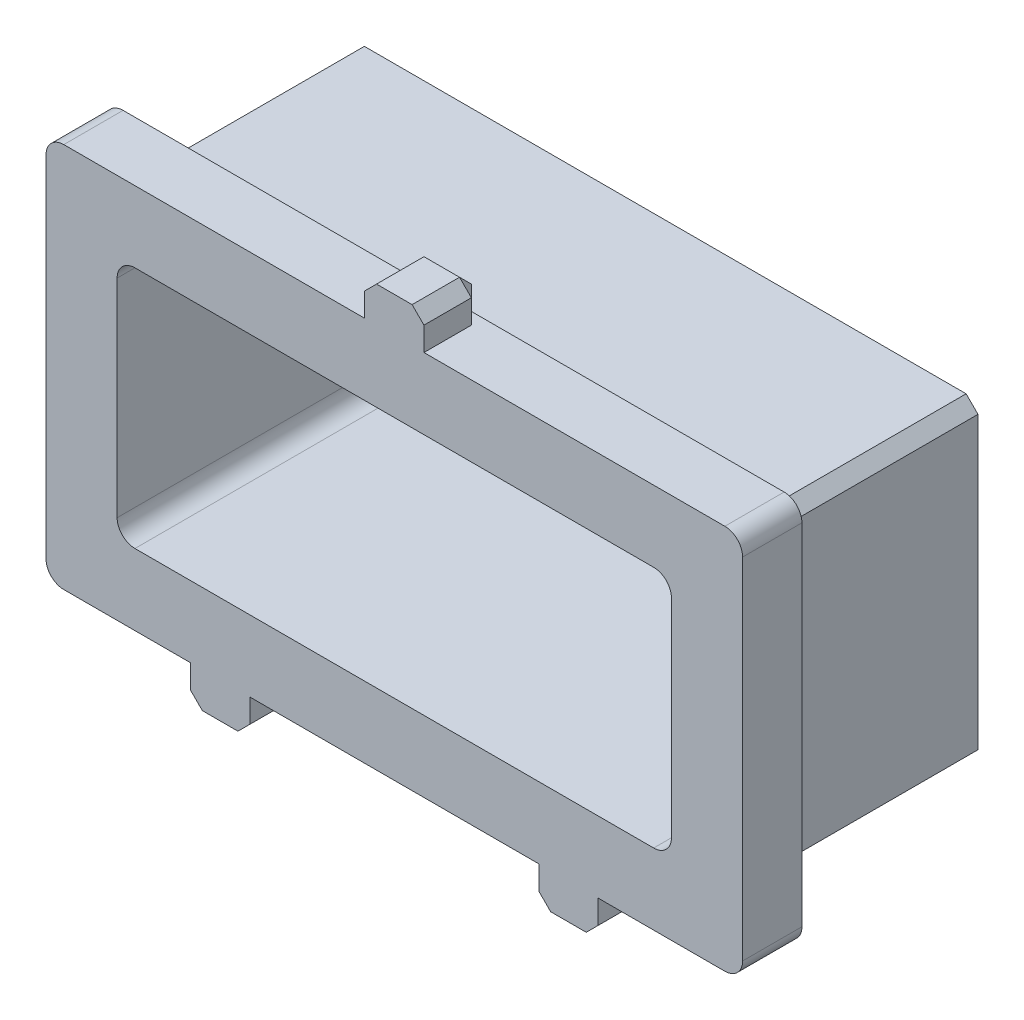
SolidWorks part; units mm, degrees
ref_plane "Front Plane" through (0, 0, 0) normal (0, 0, 1) x (1, 0, 0)
ref_plane "Top Plane" through (0, 0, 0) normal (0, 1, 0) x (1, 0, 0)
ref_plane "Right Plane" through (0, 0, 0) normal (1, 0, 0) x (0, 0, -1)
sketch "Sketch1" plane through (0, 0, 0) normal (0, 0, 1) x (1, 0, 0)
  line L4 (29.8204, 195.8186) -> (29.8204, 202.5496)
  line L5 (29.8204, 202.5496) -> (16.4219, 202.5496)
  line L6 (16.4219, 202.5496) -> (16.4219, 195.8186)
  line L7 (16.4219, 195.8186) -> (29.8204, 195.8186)
  line L8 (29.8204, 195.8186) -> (29.8204, 202.5496)
  line L9 (29.8204, 202.5496) -> (16.4219, 202.5496)
  line L10 (16.4219, 202.5496) -> (16.4219, 195.8186)
  line L11 (16.4219, 195.8186) -> (29.8204, 195.8186)
  dimension "D1" = 0
extrude "Extrude-Thin1" add sketch "Sketch1" along normal blind 5.8039 thin thin type one direction reverse wall 0.762
sketch "Sketch2" plane through (0, 0, 5.8039) normal (0, 0, 1) x (1, 0, 0)
  line L4 (16.4219, 195.8186) -> (29.8204, 195.8186)
  line L5 (29.8204, 195.8186) -> (29.8204, 202.5496)
  line L6 (29.8204, 202.5496) -> (16.4219, 202.5496)
  line L7 (16.4219, 202.5496) -> (16.4219, 195.8186)
  line L8 (16.4219, 195.8186) -> (29.8204, 195.8186)
  line L9 (29.8204, 195.8186) -> (29.8204, 202.5496)
  line L10 (29.8204, 202.5496) -> (16.4219, 202.5496)
  line L11 (16.4219, 202.5496) -> (16.4219, 195.8186)
  dimension "D1" = 0
extrude "Extrude-Thin2" add sketch "Sketch2" against normal blind 1.27 thin
sketch "Sketch4" plane through (0, 0, 5.8039) normal (0, 0, 1) x (1, 0, 0)
  line L0 (15.6599, 203.3116) -> (23.1211, 203.3116) construction
  line L1 (30.5824, 203.3116) -> (15.6599, 203.3116) construction
  line L2 (23.1211, 203.3116) -> (30.5824, 203.3116) construction
  line L3 (23.1211, 203.3116) -> (23.1211, 204.0736) construction
  line L4 (23.1211, 203.3116) -> (23.1211, 204.0736) construction
  line L5 (15.6599, 195.0566) -> (30.5824, 195.0566) construction
  line L6 (23.7561, 203.3116) -> (23.7561, 204.0736)
  line L7 (15.6599, 195.0566) -> (19.3905, 195.0566) construction
  line L8 (22.4861, 203.3116) -> (22.4861, 204.0736)
  line L9 (19.3905, 195.0566) -> (23.1211, 195.0566) construction
  line L10 (23.1211, 195.0566) -> (26.8517, 195.0566) construction
  line L11 (23.7561, 203.3116) -> (22.4861, 203.3116)
  line L12 (23.7561, 204.0736) -> (22.4861, 204.0736)
  line L13 (26.8517, 195.0566) -> (30.5824, 195.0566) construction
  line L14 (30.5824, 195.0566) -> (30.5824, 203.3116) construction
  line L16 (27.4867, 195.0566) -> (27.4867, 194.2946)
  line L17 (27.4867, 194.2946) -> (26.2167, 194.2946)
  line L18 (26.2167, 195.0566) -> (26.2167, 194.2946)
  line L19 (27.4867, 195.0566) -> (26.2167, 195.0566)
  line L20 (20.0255, 195.0566) -> (18.7555, 195.0566)
  line L21 (20.0255, 195.0566) -> (20.0255, 194.2946)
  line L22 (20.0255, 194.2946) -> (18.7555, 194.2946)
  line L23 (18.7555, 195.0566) -> (18.7555, 194.2946)
  point P11 (23.1211, 204.0736)
  dimension "D1" = 0.762
  dimension "D2" = 1.27
  dimension "D3" = 0.762
  dimension "D4" = 1.27
  dimension "D5" = 1.27
extrude "Boss-Extrude1" add sketch "Sketch4" against normal blind 1.27
chamfer "Chamfer1" distance 0.254 angle 45 21 edges at (29.8204, 195.8186, 2.2669) (16.4219, 195.8186, 2.2669) (29.8204, 202.5496, 2.2669) (16.4219, 202.5496, 2.2669) (27.4867, 194.2946, 5.1689) (26.2167, 194.2946, 5.1689) (20.0255, 194.2946, 5.1689) (18.7555, 194.2946, 5.1689) (23.7561, 204.0736, 5.1689) (22.4861, 204.0736, 5.1689) (26.8517, 194.2946, 4.5339) (18.7555, 194.6756, 4.5339) (19.3905, 194.2946, 4.5339) (20.0255, 194.6756, 4.5339) (23.1211, 204.0736, 4.5339)
fillet "Fillet1" radius 0.381 8 edges at (15.6599, 203.3116, 5.1689) (15.6599, 195.0566, 5.1689) (30.5824, 195.0566, 5.1689) (30.5824, 203.3116, 5.1689) (29.0584, 201.7876, 2.9019) (17.1839, 201.7876, 2.9019) (29.0584, 196.5806, 2.9019) (17.1839, 196.5806, 2.9019)
equation "\"D3@Sketch4\"=\"D1@Sketch4\""
equation "\"D4@Sketch4\"=\"D2@Sketch4\""
equation "\"D5@Sketch4\"=\"D2@Sketch4\""
